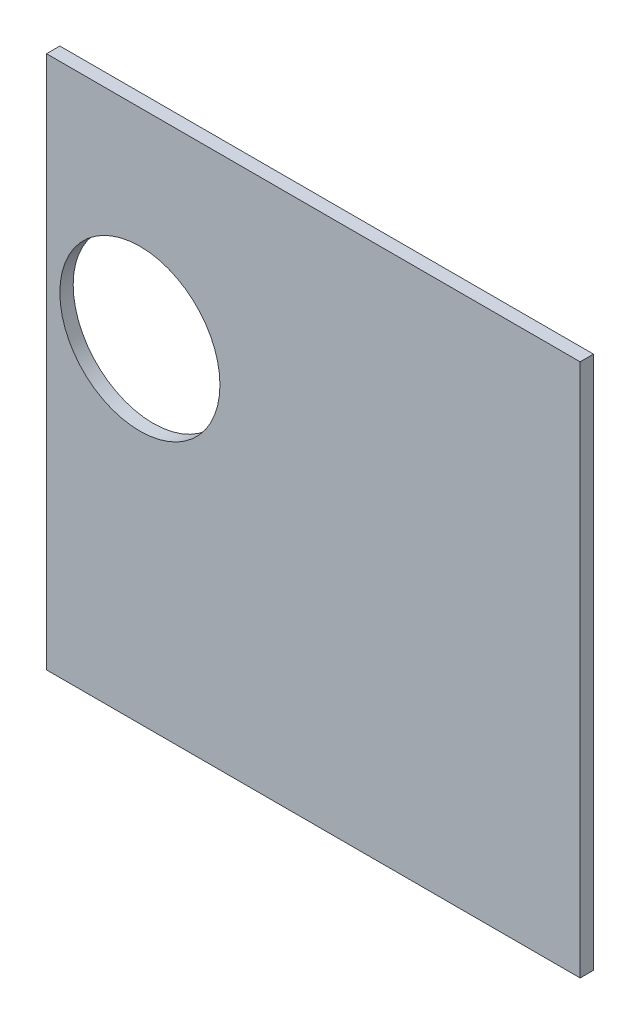
SolidWorks part; units mm, degrees
ref_plane "Front Plane" through (0, 0, 0) normal (0, 0, 1) x (1, 0, 0)
ref_plane "Top Plane" through (0, 0, 0) normal (0, 1, 0) x (1, 0, 0)
ref_plane "Right Plane" through (0, 0, 0) normal (1, 0, 0) x (0, 0, -1)
sketch "Sketch1" plane through (0, 0, 0) normal (0, 0, 1) x (1, 0, 0)
  line L1 (0, 0) -> (254, 0)
  line L2 (0, 0) -> (0, 254)
  line L3 (0, 254) -> (254, 254)
  line L4 (254, 0) -> (254, 254)
  dimension "D1" = 254
  dimension "D2" = 254
extrude "Boss-Extrude1" add sketch "Sketch1" along normal blind 6.35 contours L1 L4 L3 L2
sketch "Sketch2" plane through (0, 0, 6.35) normal (0, 0, 1) x (1, 0, 0)
  line L0 (0, 0) -> (0, 254) construction
  line L1 (0, 254) -> (254, 254) construction
  circle A0 centre (44.45, 158.75) radius 38.1
  dimension "D1" = 76.2
  dimension "D2" = 44.45
  dimension "D3" = 95.25
extrude "Cut-Extrude1" cut sketch "Sketch2" against normal through all
